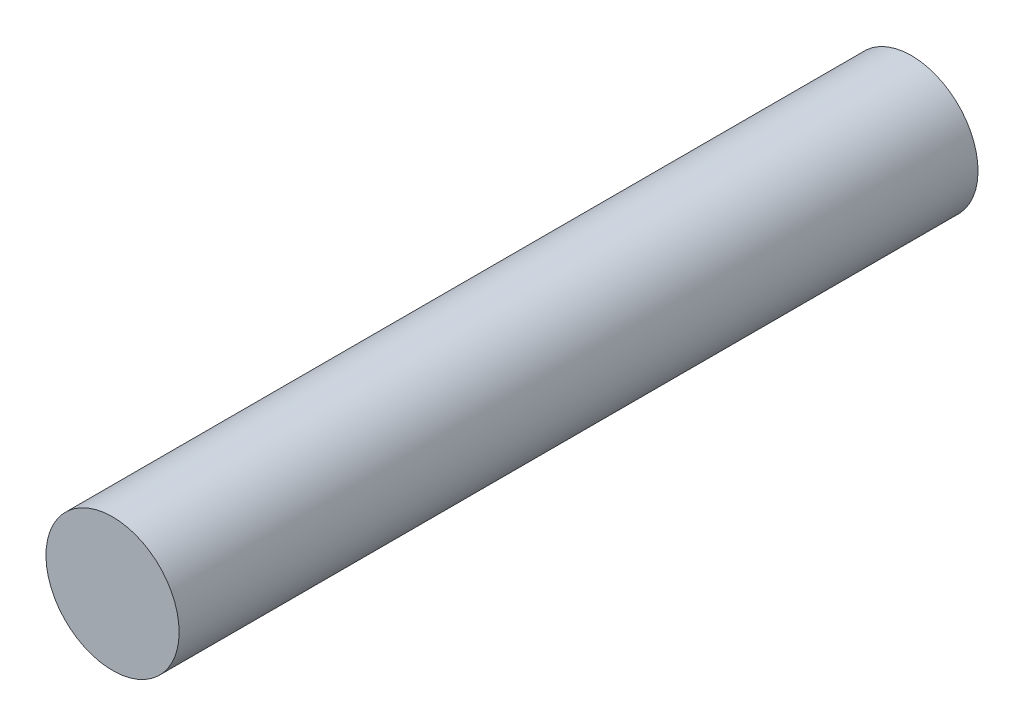
SolidWorks part; units mm, degrees
ref_plane "Front Plane" through (0, 0, 0) normal (0, 0, 1) x (1, 0, 0)
ref_plane "Top Plane" through (0, 0, 0) normal (0, 1, 0) x (1, 0, 0)
ref_plane "Right Plane" through (0, 0, 0) normal (1, 0, 0) x (0, 0, -1)
sketch "Sketch1" plane through (0, 0, 0) normal (0, 0, 1) x (1, 0, 0)
  circle A0 centre (0, 0) radius 2.5
  dimension "D1" = 5
extrude "Boss-Extrude1" add sketch "Sketch1" along normal mid plane 30
sketch "Sketch2" plane through (0, 0, -15) normal (0, 0, -1) x (-1, 0, 0)
  line L0 (-0.5, -2.4495) -> (-0.5, -1.9495)
  line L1 (-0.5, -1.9495) -> (0.5, -1.9495)
  line L2 (0.5, -1.9495) -> (0.5, -2.4495)
  circle A0 centre (0, 0) radius 2.5 construction
  arc A1 (0.5, -2.4495) -> (-0.5, -2.4495) centre (0, 0) cw
  point P4 (0, -1.9495)
  dimension "D1" = 1
  dimension "D2" = 0.5
extrude "Cut-Extrude1" cut sketch "Sketch2" against normal blind 10
